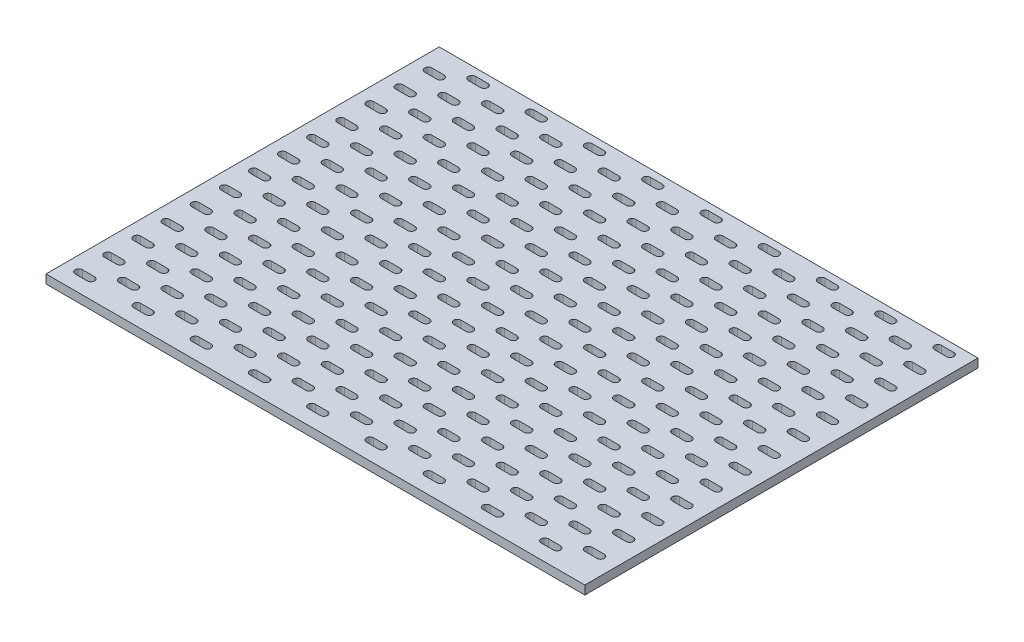
SolidWorks part; units mm, degrees
ref_plane "Спереди" through (0, 0, 0) normal (0, 0, 1) x (1, 0, 0)
ref_plane "Сверху" through (0, 0, 0) normal (0, 1, 0) x (1, 0, 0)
ref_plane "Справа" through (0, 0, 0) normal (1, 0, 0) x (0, 0, -1)
sketch "Эскиз1" plane through (0, 0, 0) normal (0, 1, 0) x (1, 0, 0)
  line L0 (-155, 130) -> (-146.6325, 130)
  line L1 (-185, 135) -> (185, 135)
  line L2 (-185, 135) -> (-185, -135)
  line L3 (-185, -135) -> (185, -135)
  line L4 (185, 135) -> (185, -135)
  line L5 (-185, 135) -> (185, -135) construction
  line L6 (-185, -135) -> (185, 135) construction
  line L7 (-155, 125) -> (-146.6325, 125)
  line L8 (-175, 115) -> (-166.6325, 115)
  line L9 (-175, 120) -> (-166.6325, 120)
  line L10 (-115, 130) -> (-106.6325, 130)
  line L11 (-115, 125) -> (-106.6325, 125)
  line L12 (-135, 115) -> (-126.6325, 115)
  line L13 (-135, 120) -> (-126.6325, 120)
  line L14 (-75, 130) -> (-66.6325, 130)
  line L15 (-75, 125) -> (-66.6325, 125)
  line L16 (-95, 115) -> (-86.6325, 115)
  line L17 (-95, 120) -> (-86.6325, 120)
  line L18 (-35, 130) -> (-26.6325, 130)
  line L19 (-35, 125) -> (-26.6325, 125)
  line L20 (-55, 115) -> (-46.6325, 115)
  line L21 (-55, 120) -> (-46.6325, 120)
  line L22 (5, 130) -> (13.3675, 130)
  line L23 (5, 125) -> (13.3675, 125)
  line L24 (-15, 115) -> (-6.6325, 115)
  line L25 (-15, 120) -> (-6.6325, 120)
  line L26 (45, 130) -> (53.3675, 130)
  line L27 (45, 125) -> (53.3675, 125)
  line L28 (25, 115) -> (33.3675, 115)
  line L29 (25, 120) -> (33.3675, 120)
  line L30 (85, 130) -> (93.3675, 130)
  line L31 (85, 125) -> (93.3675, 125)
  line L32 (65, 115) -> (73.3675, 115)
  line L33 (65, 120) -> (73.3675, 120)
  line L34 (125, 130) -> (133.3675, 130)
  line L35 (125, 125) -> (133.3675, 125)
  line L36 (105, 115) -> (113.3675, 115)
  line L37 (105, 120) -> (113.3675, 120)
  line L38 (165, 130) -> (173.3675, 130)
  line L39 (165, 125) -> (173.3675, 125)
  line L40 (145, 115) -> (153.3675, 115)
  line L41 (145, 120) -> (153.3675, 120)
  line L42 (-155, 110) -> (-146.6325, 110)
  line L43 (-155, 105) -> (-146.6325, 105)
  line L44 (-175, 95) -> (-166.6325, 95)
  line L45 (-175, 100) -> (-166.6325, 100)
  line L46 (-115, 110) -> (-106.6325, 110)
  line L47 (-115, 105) -> (-106.6325, 105)
  line L48 (-135, 95) -> (-126.6325, 95)
  line L49 (-135, 100) -> (-126.6325, 100)
  line L50 (-75, 110) -> (-66.6325, 110)
  line L51 (-75, 105) -> (-66.6325, 105)
  line L52 (-95, 95) -> (-86.6325, 95)
  line L53 (-95, 100) -> (-86.6325, 100)
  line L54 (-35, 110) -> (-26.6325, 110)
  line L55 (-35, 105) -> (-26.6325, 105)
  line L56 (-55, 95) -> (-46.6325, 95)
  line L57 (-55, 100) -> (-46.6325, 100)
  line L58 (5, 110) -> (13.3675, 110)
  line L59 (5, 105) -> (13.3675, 105)
  line L60 (-15, 95) -> (-6.6325, 95)
  line L61 (-15, 100) -> (-6.6325, 100)
  line L62 (45, 110) -> (53.3675, 110)
  line L63 (45, 105) -> (53.3675, 105)
  line L64 (25, 95) -> (33.3675, 95)
  line L65 (25, 100) -> (33.3675, 100)
  line L66 (85, 110) -> (93.3675, 110)
  line L67 (85, 105) -> (93.3675, 105)
  line L68 (65, 95) -> (73.3675, 95)
  line L69 (65, 100) -> (73.3675, 100)
  line L70 (125, 110) -> (133.3675, 110)
  line L71 (125, 105) -> (133.3675, 105)
  line L72 (105, 95) -> (113.3675, 95)
  line L73 (105, 100) -> (113.3675, 100)
  line L74 (165, 110) -> (173.3675, 110)
  line L75 (165, 105) -> (173.3675, 105)
  line L76 (145, 95) -> (153.3675, 95)
  line L77 (145, 100) -> (153.3675, 100)
  line L78 (-155, 90) -> (-146.6325, 90)
  line L79 (-155, 85) -> (-146.6325, 85)
  line L80 (-175, 75) -> (-166.6325, 75)
  line L81 (-175, 80) -> (-166.6325, 80)
  line L82 (-115, 90) -> (-106.6325, 90)
  line L83 (-115, 85) -> (-106.6325, 85)
  line L84 (-135, 75) -> (-126.6325, 75)
  line L85 (-135, 80) -> (-126.6325, 80)
  line L86 (-75, 90) -> (-66.6325, 90)
  line L87 (-75, 85) -> (-66.6325, 85)
  line L88 (-95, 75) -> (-86.6325, 75)
  line L89 (-95, 80) -> (-86.6325, 80)
  line L90 (-35, 90) -> (-26.6325, 90)
  line L91 (-35, 85) -> (-26.6325, 85)
  line L92 (-55, 75) -> (-46.6325, 75)
  line L93 (-55, 80) -> (-46.6325, 80)
  line L94 (5, 90) -> (13.3675, 90)
  line L95 (5, 85) -> (13.3675, 85)
  line L96 (-15, 75) -> (-6.6325, 75)
  line L97 (-15, 80) -> (-6.6325, 80)
  line L98 (45, 90) -> (53.3675, 90)
  line L99 (45, 85) -> (53.3675, 85)
  line L100 (25, 75) -> (33.3675, 75)
  line L101 (25, 80) -> (33.3675, 80)
  line L102 (85, 90) -> (93.3675, 90)
  line L103 (85, 85) -> (93.3675, 85)
  line L104 (65, 75) -> (73.3675, 75)
  line L105 (65, 80) -> (73.3675, 80)
  line L106 (125, 90) -> (133.3675, 90)
  line L107 (125, 85) -> (133.3675, 85)
  line L108 (105, 75) -> (113.3675, 75)
  line L109 (105, 80) -> (113.3675, 80)
  line L110 (165, 90) -> (173.3675, 90)
  line L111 (165, 85) -> (173.3675, 85)
  line L112 (145, 75) -> (153.3675, 75)
  line L113 (145, 80) -> (153.3675, 80)
  line L114 (-155, 70) -> (-146.6325, 70)
  line L115 (-155, 65) -> (-146.6325, 65)
  line L116 (-175, 55) -> (-166.6325, 55)
  line L117 (-175, 60) -> (-166.6325, 60)
  line L118 (-115, 70) -> (-106.6325, 70)
  line L119 (-115, 65) -> (-106.6325, 65)
  line L120 (-135, 55) -> (-126.6325, 55)
  line L121 (-135, 60) -> (-126.6325, 60)
  line L122 (-75, 70) -> (-66.6325, 70)
  line L123 (-75, 65) -> (-66.6325, 65)
  line L124 (-95, 55) -> (-86.6325, 55)
  line L125 (-95, 60) -> (-86.6325, 60)
  line L126 (-35, 70) -> (-26.6325, 70)
  line L127 (-35, 65) -> (-26.6325, 65)
  line L128 (-55, 55) -> (-46.6325, 55)
  line L129 (-55, 60) -> (-46.6325, 60)
  line L130 (5, 70) -> (13.3675, 70)
  line L131 (5, 65) -> (13.3675, 65)
  line L132 (-15, 55) -> (-6.6325, 55)
  line L133 (-15, 60) -> (-6.6325, 60)
  line L134 (45, 70) -> (53.3675, 70)
  line L135 (45, 65) -> (53.3675, 65)
  line L136 (25, 55) -> (33.3675, 55)
  line L137 (25, 60) -> (33.3675, 60)
  line L138 (85, 70) -> (93.3675, 70)
  line L139 (85, 65) -> (93.3675, 65)
  line L140 (65, 55) -> (73.3675, 55)
  line L141 (65, 60) -> (73.3675, 60)
  line L142 (125, 70) -> (133.3675, 70)
  line L143 (125, 65) -> (133.3675, 65)
  line L144 (105, 55) -> (113.3675, 55)
  line L145 (105, 60) -> (113.3675, 60)
  line L146 (165, 70) -> (173.3675, 70)
  line L147 (165, 65) -> (173.3675, 65)
  line L148 (145, 55) -> (153.3675, 55)
  line L149 (145, 60) -> (153.3675, 60)
  line L150 (-155, 50) -> (-146.6325, 50)
  line L151 (-155, 45) -> (-146.6325, 45)
  line L152 (-175, 35) -> (-166.6325, 35)
  line L153 (-175, 40) -> (-166.6325, 40)
  line L154 (-115, 50) -> (-106.6325, 50)
  line L155 (-115, 45) -> (-106.6325, 45)
  line L156 (-135, 35) -> (-126.6325, 35)
  line L157 (-135, 40) -> (-126.6325, 40)
  line L158 (-75, 50) -> (-66.6325, 50)
  line L159 (-75, 45) -> (-66.6325, 45)
  line L160 (-95, 35) -> (-86.6325, 35)
  line L161 (-95, 40) -> (-86.6325, 40)
  line L162 (-35, 50) -> (-26.6325, 50)
  line L163 (-35, 45) -> (-26.6325, 45)
  line L164 (-55, 35) -> (-46.6325, 35)
  line L165 (-55, 40) -> (-46.6325, 40)
  line L166 (5, 50) -> (13.3675, 50)
  line L167 (5, 45) -> (13.3675, 45)
  line L168 (-15, 35) -> (-6.6325, 35)
  line L169 (-15, 40) -> (-6.6325, 40)
  line L170 (45, 50) -> (53.3675, 50)
  line L171 (45, 45) -> (53.3675, 45)
  line L172 (25, 35) -> (33.3675, 35)
  line L173 (25, 40) -> (33.3675, 40)
  line L174 (85, 50) -> (93.3675, 50)
  line L175 (85, 45) -> (93.3675, 45)
  line L176 (65, 35) -> (73.3675, 35)
  line L177 (65, 40) -> (73.3675, 40)
  line L178 (125, 50) -> (133.3675, 50)
  line L179 (125, 45) -> (133.3675, 45)
  line L180 (105, 35) -> (113.3675, 35)
  line L181 (105, 40) -> (113.3675, 40)
  line L182 (165, 50) -> (173.3675, 50)
  line L183 (165, 45) -> (173.3675, 45)
  line L184 (145, 35) -> (153.3675, 35)
  line L185 (145, 40) -> (153.3675, 40)
  line L186 (-155, 30) -> (-146.6325, 30)
  line L187 (-155, 25) -> (-146.6325, 25)
  line L188 (-175, 15) -> (-166.6325, 15)
  line L189 (-175, 20) -> (-166.6325, 20)
  line L190 (-115, 30) -> (-106.6325, 30)
  line L191 (-115, 25) -> (-106.6325, 25)
  line L192 (-135, 15) -> (-126.6325, 15)
  line L193 (-135, 20) -> (-126.6325, 20)
  line L194 (-75, 30) -> (-66.6325, 30)
  line L195 (-75, 25) -> (-66.6325, 25)
  line L196 (-95, 15) -> (-86.6325, 15)
  line L197 (-95, 20) -> (-86.6325, 20)
  line L198 (-35, 30) -> (-26.6325, 30)
  line L199 (-35, 25) -> (-26.6325, 25)
  line L200 (-55, 15) -> (-46.6325, 15)
  line L201 (-55, 20) -> (-46.6325, 20)
  line L202 (5, 30) -> (13.3675, 30)
  line L203 (5, 25) -> (13.3675, 25)
  line L204 (-15, 15) -> (-6.6325, 15)
  line L205 (-15, 20) -> (-6.6325, 20)
  line L206 (45, 30) -> (53.3675, 30)
  line L207 (45, 25) -> (53.3675, 25)
  line L208 (25, 15) -> (33.3675, 15)
  line L209 (25, 20) -> (33.3675, 20)
  line L210 (85, 30) -> (93.3675, 30)
  line L211 (85, 25) -> (93.3675, 25)
  line L212 (65, 15) -> (73.3675, 15)
  line L213 (65, 20) -> (73.3675, 20)
  line L214 (125, 30) -> (133.3675, 30)
  line L215 (125, 25) -> (133.3675, 25)
  line L216 (105, 15) -> (113.3675, 15)
  line L217 (105, 20) -> (113.3675, 20)
  line L218 (165, 30) -> (173.3675, 30)
  line L219 (165, 25) -> (173.3675, 25)
  line L220 (145, 15) -> (153.3675, 15)
  line L221 (145, 20) -> (153.3675, 20)
  line L222 (-155, 10) -> (-146.6325, 10)
  line L223 (-155, 5) -> (-146.6325, 5)
  line L224 (-175, -5) -> (-166.6325, -5)
  line L225 (-175, 0) -> (-166.6325, 0)
  line L226 (-115, 10) -> (-106.6325, 10)
  line L227 (-115, 5) -> (-106.6325, 5)
  line L228 (-135, -5) -> (-126.6325, -5)
  line L229 (-135, 0) -> (-126.6325, 0)
  line L230 (-75, 10) -> (-66.6325, 10)
  line L231 (-75, 5) -> (-66.6325, 5)
  line L232 (-95, -5) -> (-86.6325, -5)
  line L233 (-95, 0) -> (-86.6325, 0)
  line L234 (-35, 10) -> (-26.6325, 10)
  line L235 (-35, 5) -> (-26.6325, 5)
  line L236 (-55, -5) -> (-46.6325, -5)
  line L237 (-55, 0) -> (-46.6325, 0)
  line L238 (5, 10) -> (13.3675, 10)
  line L239 (5, 5) -> (13.3675, 5)
  line L240 (-15, -5) -> (-6.6325, -5)
  line L241 (-15, 0) -> (-6.6325, 0)
  line L242 (45, 10) -> (53.3675, 10)
  line L243 (45, 5) -> (53.3675, 5)
  line L244 (25, -5) -> (33.3675, -5)
  line L245 (25, 0) -> (33.3675, 0)
  line L246 (85, 10) -> (93.3675, 10)
  line L247 (85, 5) -> (93.3675, 5)
  line L248 (65, -5) -> (73.3675, -5)
  line L249 (65, 0) -> (73.3675, 0)
  line L250 (125, 10) -> (133.3675, 10)
  line L251 (125, 5) -> (133.3675, 5)
  line L252 (105, -5) -> (113.3675, -5)
  line L253 (105, 0) -> (113.3675, 0)
  line L254 (165, 10) -> (173.3675, 10)
  line L255 (165, 5) -> (173.3675, 5)
  line L256 (145, -5) -> (153.3675, -5)
  line L257 (145, 0) -> (153.3675, 0)
  line L258 (-155, -10) -> (-146.6325, -10)
  line L259 (-155, -15) -> (-146.6325, -15)
  line L260 (-175, -25) -> (-166.6325, -25)
  line L261 (-175, -20) -> (-166.6325, -20)
  line L262 (-115, -10) -> (-106.6325, -10)
  line L263 (-115, -15) -> (-106.6325, -15)
  line L264 (-135, -25) -> (-126.6325, -25)
  line L265 (-135, -20) -> (-126.6325, -20)
  line L266 (-75, -10) -> (-66.6325, -10)
  line L267 (-75, -15) -> (-66.6325, -15)
  line L268 (-95, -25) -> (-86.6325, -25)
  line L269 (-95, -20) -> (-86.6325, -20)
  line L270 (-35, -10) -> (-26.6325, -10)
  line L271 (-35, -15) -> (-26.6325, -15)
  line L272 (-55, -25) -> (-46.6325, -25)
  line L273 (-55, -20) -> (-46.6325, -20)
  line L274 (5, -10) -> (13.3675, -10)
  line L275 (5, -15) -> (13.3675, -15)
  line L276 (-15, -25) -> (-6.6325, -25)
  line L277 (-15, -20) -> (-6.6325, -20)
  line L278 (45, -10) -> (53.3675, -10)
  line L279 (45, -15) -> (53.3675, -15)
  line L280 (25, -25) -> (33.3675, -25)
  line L281 (25, -20) -> (33.3675, -20)
  line L282 (85, -10) -> (93.3675, -10)
  line L283 (85, -15) -> (93.3675, -15)
  line L284 (65, -25) -> (73.3675, -25)
  line L285 (65, -20) -> (73.3675, -20)
  line L286 (125, -10) -> (133.3675, -10)
  line L287 (125, -15) -> (133.3675, -15)
  line L288 (105, -25) -> (113.3675, -25)
  line L289 (105, -20) -> (113.3675, -20)
  line L290 (165, -10) -> (173.3675, -10)
  line L291 (165, -15) -> (173.3675, -15)
  line L292 (145, -25) -> (153.3675, -25)
  line L293 (145, -20) -> (153.3675, -20)
  line L294 (-155, -30) -> (-146.6325, -30)
  line L295 (-155, -35) -> (-146.6325, -35)
  line L296 (-175, -45) -> (-166.6325, -45)
  line L297 (-175, -40) -> (-166.6325, -40)
  line L298 (-115, -30) -> (-106.6325, -30)
  line L299 (-115, -35) -> (-106.6325, -35)
  line L300 (-135, -45) -> (-126.6325, -45)
  line L301 (-135, -40) -> (-126.6325, -40)
  line L302 (-75, -30) -> (-66.6325, -30)
  line L303 (-75, -35) -> (-66.6325, -35)
  line L304 (-95, -45) -> (-86.6325, -45)
  line L305 (-95, -40) -> (-86.6325, -40)
  line L306 (-35, -30) -> (-26.6325, -30)
  line L307 (-35, -35) -> (-26.6325, -35)
  line L308 (-55, -45) -> (-46.6325, -45)
  line L309 (-55, -40) -> (-46.6325, -40)
  line L310 (5, -30) -> (13.3675, -30)
  line L311 (5, -35) -> (13.3675, -35)
  line L312 (-15, -45) -> (-6.6325, -45)
  line L313 (-15, -40) -> (-6.6325, -40)
  line L314 (45, -30) -> (53.3675, -30)
  line L315 (45, -35) -> (53.3675, -35)
  line L316 (25, -45) -> (33.3675, -45)
  line L317 (25, -40) -> (33.3675, -40)
  line L318 (85, -30) -> (93.3675, -30)
  line L319 (85, -35) -> (93.3675, -35)
  line L320 (65, -45) -> (73.3675, -45)
  line L321 (65, -40) -> (73.3675, -40)
  line L322 (125, -30) -> (133.3675, -30)
  line L323 (125, -35) -> (133.3675, -35)
  line L324 (105, -45) -> (113.3675, -45)
  line L325 (105, -40) -> (113.3675, -40)
  line L326 (165, -30) -> (173.3675, -30)
  line L327 (165, -35) -> (173.3675, -35)
  line L328 (145, -45) -> (153.3675, -45)
  line L329 (145, -40) -> (153.3675, -40)
  line L330 (-155, -50) -> (-146.6325, -50)
  line L331 (-155, -55) -> (-146.6325, -55)
  line L332 (-175, -65) -> (-166.6325, -65)
  line L333 (-175, -60) -> (-166.6325, -60)
  line L334 (-115, -50) -> (-106.6325, -50)
  line L335 (-115, -55) -> (-106.6325, -55)
  line L336 (-135, -65) -> (-126.6325, -65)
  line L337 (-135, -60) -> (-126.6325, -60)
  line L338 (-75, -50) -> (-66.6325, -50)
  line L339 (-75, -55) -> (-66.6325, -55)
  line L340 (-95, -65) -> (-86.6325, -65)
  line L341 (-95, -60) -> (-86.6325, -60)
  line L342 (-35, -50) -> (-26.6325, -50)
  line L343 (-35, -55) -> (-26.6325, -55)
  line L344 (-55, -65) -> (-46.6325, -65)
  line L345 (-55, -60) -> (-46.6325, -60)
  line L346 (5, -50) -> (13.3675, -50)
  line L347 (5, -55) -> (13.3675, -55)
  line L348 (-15, -65) -> (-6.6325, -65)
  line L349 (-15, -60) -> (-6.6325, -60)
  line L350 (45, -50) -> (53.3675, -50)
  line L351 (45, -55) -> (53.3675, -55)
  line L352 (25, -65) -> (33.3675, -65)
  line L353 (25, -60) -> (33.3675, -60)
  line L354 (85, -50) -> (93.3675, -50)
  line L355 (85, -55) -> (93.3675, -55)
  line L356 (65, -65) -> (73.3675, -65)
  line L357 (65, -60) -> (73.3675, -60)
  line L358 (125, -50) -> (133.3675, -50)
  line L359 (125, -55) -> (133.3675, -55)
  line L360 (105, -65) -> (113.3675, -65)
  line L361 (105, -60) -> (113.3675, -60)
  line L362 (165, -50) -> (173.3675, -50)
  line L363 (165, -55) -> (173.3675, -55)
  line L364 (145, -65) -> (153.3675, -65)
  line L365 (145, -60) -> (153.3675, -60)
  line L366 (-155, -70) -> (-146.6325, -70)
  line L367 (-155, -75) -> (-146.6325, -75)
  line L368 (-175, -85) -> (-166.6325, -85)
  line L369 (-175, -80) -> (-166.6325, -80)
  line L370 (-115, -70) -> (-106.6325, -70)
  line L371 (-115, -75) -> (-106.6325, -75)
  line L372 (-135, -85) -> (-126.6325, -85)
  line L373 (-135, -80) -> (-126.6325, -80)
  line L374 (-75, -70) -> (-66.6325, -70)
  line L375 (-75, -75) -> (-66.6325, -75)
  line L376 (-95, -85) -> (-86.6325, -85)
  line L377 (-95, -80) -> (-86.6325, -80)
  line L378 (-35, -70) -> (-26.6325, -70)
  line L379 (-35, -75) -> (-26.6325, -75)
  line L380 (-55, -85) -> (-46.6325, -85)
  line L381 (-55, -80) -> (-46.6325, -80)
  line L382 (5, -70) -> (13.3675, -70)
  line L383 (5, -75) -> (13.3675, -75)
  line L384 (-15, -85) -> (-6.6325, -85)
  line L385 (-15, -80) -> (-6.6325, -80)
  line L386 (45, -70) -> (53.3675, -70)
  line L387 (45, -75) -> (53.3675, -75)
  line L388 (25, -85) -> (33.3675, -85)
  line L389 (25, -80) -> (33.3675, -80)
  line L390 (85, -70) -> (93.3675, -70)
  line L391 (85, -75) -> (93.3675, -75)
  line L392 (65, -85) -> (73.3675, -85)
  line L393 (65, -80) -> (73.3675, -80)
  line L394 (125, -70) -> (133.3675, -70)
  line L395 (125, -75) -> (133.3675, -75)
  line L396 (105, -85) -> (113.3675, -85)
  line L397 (105, -80) -> (113.3675, -80)
  line L398 (165, -70) -> (173.3675, -70)
  line L399 (165, -75) -> (173.3675, -75)
  line L400 (145, -85) -> (153.3675, -85)
  line L401 (145, -80) -> (153.3675, -80)
  line L402 (-155, -90) -> (-146.6325, -90)
  line L403 (-155, -95) -> (-146.6325, -95)
  line L404 (-175, -105) -> (-166.6325, -105)
  line L405 (-175, -100) -> (-166.6325, -100)
  line L406 (-115, -90) -> (-106.6325, -90)
  line L407 (-115, -95) -> (-106.6325, -95)
  line L408 (-135, -105) -> (-126.6325, -105)
  line L409 (-135, -100) -> (-126.6325, -100)
  line L410 (-75, -90) -> (-66.6325, -90)
  line L411 (-75, -95) -> (-66.6325, -95)
  line L412 (-95, -105) -> (-86.6325, -105)
  line L413 (-95, -100) -> (-86.6325, -100)
  line L414 (-35, -90) -> (-26.6325, -90)
  line L415 (-35, -95) -> (-26.6325, -95)
  line L416 (-55, -105) -> (-46.6325, -105)
  line L417 (-55, -100) -> (-46.6325, -100)
  line L418 (5, -90) -> (13.3675, -90)
  line L419 (5, -95) -> (13.3675, -95)
  line L420 (-15, -105) -> (-6.6325, -105)
  line L421 (-15, -100) -> (-6.6325, -100)
  line L422 (45, -90) -> (53.3675, -90)
  line L423 (45, -95) -> (53.3675, -95)
  line L424 (25, -105) -> (33.3675, -105)
  line L425 (25, -100) -> (33.3675, -100)
  line L426 (85, -90) -> (93.3675, -90)
  line L427 (85, -95) -> (93.3675, -95)
  line L428 (65, -105) -> (73.3675, -105)
  line L429 (65, -100) -> (73.3675, -100)
  line L430 (125, -90) -> (133.3675, -90)
  line L431 (125, -95) -> (133.3675, -95)
  line L432 (105, -105) -> (113.3675, -105)
  line L433 (105, -100) -> (113.3675, -100)
  line L434 (165, -90) -> (173.3675, -90)
  line L435 (165, -95) -> (173.3675, -95)
  line L436 (145, -105) -> (153.3675, -105)
  line L437 (145, -100) -> (153.3675, -100)
  line L438 (-155, -110) -> (-146.6325, -110)
  line L439 (-155, -115) -> (-146.6325, -115)
  line L440 (-175, -125) -> (-166.6325, -125)
  line L441 (-175, -120) -> (-166.6325, -120)
  line L442 (-115, -110) -> (-106.6325, -110)
  line L443 (-115, -115) -> (-106.6325, -115)
  line L444 (-135, -125) -> (-126.6325, -125)
  line L445 (-135, -120) -> (-126.6325, -120)
  line L446 (-75, -110) -> (-66.6325, -110)
  line L447 (-75, -115) -> (-66.6325, -115)
  line L448 (-95, -125) -> (-86.6325, -125)
  line L449 (-95, -120) -> (-86.6325, -120)
  line L450 (-35, -110) -> (-26.6325, -110)
  line L451 (-35, -115) -> (-26.6325, -115)
  line L452 (-55, -125) -> (-46.6325, -125)
  line L453 (-55, -120) -> (-46.6325, -120)
  line L454 (5, -110) -> (13.3675, -110)
  line L455 (5, -115) -> (13.3675, -115)
  line L456 (-15, -125) -> (-6.6325, -125)
  line L457 (-15, -120) -> (-6.6325, -120)
  line L458 (45, -110) -> (53.3675, -110)
  line L459 (45, -115) -> (53.3675, -115)
  line L460 (25, -125) -> (33.3675, -125)
  line L461 (25, -120) -> (33.3675, -120)
  line L462 (85, -110) -> (93.3675, -110)
  line L463 (85, -115) -> (93.3675, -115)
  line L464 (65, -125) -> (73.3675, -125)
  line L465 (65, -120) -> (73.3675, -120)
  line L466 (125, -110) -> (133.3675, -110)
  line L467 (125, -115) -> (133.3675, -115)
  line L468 (105, -125) -> (113.3675, -125)
  line L469 (105, -120) -> (113.3675, -120)
  line L470 (165, -110) -> (173.3675, -110)
  line L471 (165, -115) -> (173.3675, -115)
  line L472 (145, -125) -> (153.3675, -125)
  line L473 (145, -120) -> (153.3675, -120)
  arc A0 (-146.6325, 125) -> (-146.6325, 130) centre (-146.6325, 127.5) ccw
  arc A1 (-155, 130) -> (-155, 125) centre (-155, 127.5) ccw
  arc A2 (-175, 120) -> (-175, 115) centre (-175, 117.5) ccw
  arc A3 (-166.6325, 115) -> (-166.6325, 120) centre (-166.6325, 117.5) ccw
  arc A4 (-106.6325, 125) -> (-106.6325, 130) centre (-106.6325, 127.5) ccw
  arc A5 (-115, 130) -> (-115, 125) centre (-115, 127.5) ccw
  arc A6 (-135, 120) -> (-135, 115) centre (-135, 117.5) ccw
  arc A7 (-126.6325, 115) -> (-126.6325, 120) centre (-126.6325, 117.5) ccw
  arc A8 (-66.6325, 125) -> (-66.6325, 130) centre (-66.6325, 127.5) ccw
  arc A9 (-75, 130) -> (-75, 125) centre (-75, 127.5) ccw
  arc A10 (-95, 120) -> (-95, 115) centre (-95, 117.5) ccw
  arc A11 (-86.6325, 115) -> (-86.6325, 120) centre (-86.6325, 117.5) ccw
  arc A12 (-26.6325, 125) -> (-26.6325, 130) centre (-26.6325, 127.5) ccw
  arc A13 (-35, 130) -> (-35, 125) centre (-35, 127.5) ccw
  arc A14 (-55, 120) -> (-55, 115) centre (-55, 117.5) ccw
  arc A15 (-46.6325, 115) -> (-46.6325, 120) centre (-46.6325, 117.5) ccw
  arc A16 (13.3675, 125) -> (13.3675, 130) centre (13.3675, 127.5) ccw
  arc A17 (5, 130) -> (5, 125) centre (5, 127.5) ccw
  arc A18 (-15, 120) -> (-15, 115) centre (-15, 117.5) ccw
  arc A19 (-6.6325, 115) -> (-6.6325, 120) centre (-6.6325, 117.5) ccw
  arc A20 (53.3675, 125) -> (53.3675, 130) centre (53.3675, 127.5) ccw
  arc A21 (45, 130) -> (45, 125) centre (45, 127.5) ccw
  arc A22 (25, 120) -> (25, 115) centre (25, 117.5) ccw
  arc A23 (33.3675, 115) -> (33.3675, 120) centre (33.3675, 117.5) ccw
  arc A24 (93.3675, 125) -> (93.3675, 130) centre (93.3675, 127.5) ccw
  arc A25 (85, 130) -> (85, 125) centre (85, 127.5) ccw
  arc A26 (65, 120) -> (65, 115) centre (65, 117.5) ccw
  arc A27 (73.3675, 115) -> (73.3675, 120) centre (73.3675, 117.5) ccw
  arc A28 (133.3675, 125) -> (133.3675, 130) centre (133.3675, 127.5) ccw
  arc A29 (125, 130) -> (125, 125) centre (125, 127.5) ccw
  arc A30 (105, 120) -> (105, 115) centre (105, 117.5) ccw
  arc A31 (113.3675, 115) -> (113.3675, 120) centre (113.3675, 117.5) ccw
  arc A32 (173.3675, 125) -> (173.3675, 130) centre (173.3675, 127.5) ccw
  arc A33 (165, 130) -> (165, 125) centre (165, 127.5) ccw
  arc A34 (145, 120) -> (145, 115) centre (145, 117.5) ccw
  arc A35 (153.3675, 115) -> (153.3675, 120) centre (153.3675, 117.5) ccw
  arc A36 (-146.6325, 105) -> (-146.6325, 110) centre (-146.6325, 107.5) ccw
  arc A37 (-155, 110) -> (-155, 105) centre (-155, 107.5) ccw
  arc A38 (-175, 100) -> (-175, 95) centre (-175, 97.5) ccw
  arc A39 (-166.6325, 95) -> (-166.6325, 100) centre (-166.6325, 97.5) ccw
  arc A40 (-106.6325, 105) -> (-106.6325, 110) centre (-106.6325, 107.5) ccw
  arc A41 (-115, 110) -> (-115, 105) centre (-115, 107.5) ccw
  arc A42 (-135, 100) -> (-135, 95) centre (-135, 97.5) ccw
  arc A43 (-126.6325, 95) -> (-126.6325, 100) centre (-126.6325, 97.5) ccw
  arc A44 (-66.6325, 105) -> (-66.6325, 110) centre (-66.6325, 107.5) ccw
  arc A45 (-75, 110) -> (-75, 105) centre (-75, 107.5) ccw
  arc A46 (-95, 100) -> (-95, 95) centre (-95, 97.5) ccw
  arc A47 (-86.6325, 95) -> (-86.6325, 100) centre (-86.6325, 97.5) ccw
  arc A48 (-26.6325, 105) -> (-26.6325, 110) centre (-26.6325, 107.5) ccw
  arc A49 (-35, 110) -> (-35, 105) centre (-35, 107.5) ccw
  arc A50 (-55, 100) -> (-55, 95) centre (-55, 97.5) ccw
  arc A51 (-46.6325, 95) -> (-46.6325, 100) centre (-46.6325, 97.5) ccw
  arc A52 (13.3675, 105) -> (13.3675, 110) centre (13.3675, 107.5) ccw
  arc A53 (5, 110) -> (5, 105) centre (5, 107.5) ccw
  arc A54 (-15, 100) -> (-15, 95) centre (-15, 97.5) ccw
  arc A55 (-6.6325, 95) -> (-6.6325, 100) centre (-6.6325, 97.5) ccw
  arc A56 (53.3675, 105) -> (53.3675, 110) centre (53.3675, 107.5) ccw
  arc A57 (45, 110) -> (45, 105) centre (45, 107.5) ccw
  arc A58 (25, 100) -> (25, 95) centre (25, 97.5) ccw
  arc A59 (33.3675, 95) -> (33.3675, 100) centre (33.3675, 97.5) ccw
  arc A60 (93.3675, 105) -> (93.3675, 110) centre (93.3675, 107.5) ccw
  arc A61 (85, 110) -> (85, 105) centre (85, 107.5) ccw
  arc A62 (65, 100) -> (65, 95) centre (65, 97.5) ccw
  arc A63 (73.3675, 95) -> (73.3675, 100) centre (73.3675, 97.5) ccw
  arc A64 (133.3675, 105) -> (133.3675, 110) centre (133.3675, 107.5) ccw
  arc A65 (125, 110) -> (125, 105) centre (125, 107.5) ccw
  arc A66 (105, 100) -> (105, 95) centre (105, 97.5) ccw
  arc A67 (113.3675, 95) -> (113.3675, 100) centre (113.3675, 97.5) ccw
  arc A68 (173.3675, 105) -> (173.3675, 110) centre (173.3675, 107.5) ccw
  arc A69 (165, 110) -> (165, 105) centre (165, 107.5) ccw
  arc A70 (145, 100) -> (145, 95) centre (145, 97.5) ccw
  arc A71 (153.3675, 95) -> (153.3675, 100) centre (153.3675, 97.5) ccw
  arc A72 (-146.6325, 85) -> (-146.6325, 90) centre (-146.6325, 87.5) ccw
  arc A73 (-155, 90) -> (-155, 85) centre (-155, 87.5) ccw
  arc A74 (-175, 80) -> (-175, 75) centre (-175, 77.5) ccw
  arc A75 (-166.6325, 75) -> (-166.6325, 80) centre (-166.6325, 77.5) ccw
  arc A76 (-106.6325, 85) -> (-106.6325, 90) centre (-106.6325, 87.5) ccw
  arc A77 (-115, 90) -> (-115, 85) centre (-115, 87.5) ccw
  arc A78 (-135, 80) -> (-135, 75) centre (-135, 77.5) ccw
  arc A79 (-126.6325, 75) -> (-126.6325, 80) centre (-126.6325, 77.5) ccw
  arc A80 (-66.6325, 85) -> (-66.6325, 90) centre (-66.6325, 87.5) ccw
  arc A81 (-75, 90) -> (-75, 85) centre (-75, 87.5) ccw
  arc A82 (-95, 80) -> (-95, 75) centre (-95, 77.5) ccw
  arc A83 (-86.6325, 75) -> (-86.6325, 80) centre (-86.6325, 77.5) ccw
  arc A84 (-26.6325, 85) -> (-26.6325, 90) centre (-26.6325, 87.5) ccw
  arc A85 (-35, 90) -> (-35, 85) centre (-35, 87.5) ccw
  arc A86 (-55, 80) -> (-55, 75) centre (-55, 77.5) ccw
  arc A87 (-46.6325, 75) -> (-46.6325, 80) centre (-46.6325, 77.5) ccw
  arc A88 (13.3675, 85) -> (13.3675, 90) centre (13.3675, 87.5) ccw
  arc A89 (5, 90) -> (5, 85) centre (5, 87.5) ccw
  arc A90 (-15, 80) -> (-15, 75) centre (-15, 77.5) ccw
  arc A91 (-6.6325, 75) -> (-6.6325, 80) centre (-6.6325, 77.5) ccw
  arc A92 (53.3675, 85) -> (53.3675, 90) centre (53.3675, 87.5) ccw
  arc A93 (45, 90) -> (45, 85) centre (45, 87.5) ccw
  arc A94 (25, 80) -> (25, 75) centre (25, 77.5) ccw
  arc A95 (33.3675, 75) -> (33.3675, 80) centre (33.3675, 77.5) ccw
  arc A96 (93.3675, 85) -> (93.3675, 90) centre (93.3675, 87.5) ccw
  arc A97 (85, 90) -> (85, 85) centre (85, 87.5) ccw
  arc A98 (65, 80) -> (65, 75) centre (65, 77.5) ccw
  arc A99 (73.3675, 75) -> (73.3675, 80) centre (73.3675, 77.5) ccw
  arc A100 (133.3675, 85) -> (133.3675, 90) centre (133.3675, 87.5) ccw
  arc A101 (125, 90) -> (125, 85) centre (125, 87.5) ccw
  arc A102 (105, 80) -> (105, 75) centre (105, 77.5) ccw
  arc A103 (113.3675, 75) -> (113.3675, 80) centre (113.3675, 77.5) ccw
  arc A104 (173.3675, 85) -> (173.3675, 90) centre (173.3675, 87.5) ccw
  arc A105 (165, 90) -> (165, 85) centre (165, 87.5) ccw
  arc A106 (145, 80) -> (145, 75) centre (145, 77.5) ccw
  arc A107 (153.3675, 75) -> (153.3675, 80) centre (153.3675, 77.5) ccw
  arc A108 (-146.6325, 65) -> (-146.6325, 70) centre (-146.6325, 67.5) ccw
  arc A109 (-155, 70) -> (-155, 65) centre (-155, 67.5) ccw
  arc A110 (-175, 60) -> (-175, 55) centre (-175, 57.5) ccw
  arc A111 (-166.6325, 55) -> (-166.6325, 60) centre (-166.6325, 57.5) ccw
  arc A112 (-106.6325, 65) -> (-106.6325, 70) centre (-106.6325, 67.5) ccw
  arc A113 (-115, 70) -> (-115, 65) centre (-115, 67.5) ccw
  arc A114 (-135, 60) -> (-135, 55) centre (-135, 57.5) ccw
  arc A115 (-126.6325, 55) -> (-126.6325, 60) centre (-126.6325, 57.5) ccw
  arc A116 (-66.6325, 65) -> (-66.6325, 70) centre (-66.6325, 67.5) ccw
  arc A117 (-75, 70) -> (-75, 65) centre (-75, 67.5) ccw
  arc A118 (-95, 60) -> (-95, 55) centre (-95, 57.5) ccw
  arc A119 (-86.6325, 55) -> (-86.6325, 60) centre (-86.6325, 57.5) ccw
  arc A120 (-26.6325, 65) -> (-26.6325, 70) centre (-26.6325, 67.5) ccw
  arc A121 (-35, 70) -> (-35, 65) centre (-35, 67.5) ccw
  arc A122 (-55, 60) -> (-55, 55) centre (-55, 57.5) ccw
  arc A123 (-46.6325, 55) -> (-46.6325, 60) centre (-46.6325, 57.5) ccw
  arc A124 (13.3675, 65) -> (13.3675, 70) centre (13.3675, 67.5) ccw
  arc A125 (5, 70) -> (5, 65) centre (5, 67.5) ccw
  arc A126 (-15, 60) -> (-15, 55) centre (-15, 57.5) ccw
  arc A127 (-6.6325, 55) -> (-6.6325, 60) centre (-6.6325, 57.5) ccw
  arc A128 (53.3675, 65) -> (53.3675, 70) centre (53.3675, 67.5) ccw
  arc A129 (45, 70) -> (45, 65) centre (45, 67.5) ccw
  arc A130 (25, 60) -> (25, 55) centre (25, 57.5) ccw
  arc A131 (33.3675, 55) -> (33.3675, 60) centre (33.3675, 57.5) ccw
  arc A132 (93.3675, 65) -> (93.3675, 70) centre (93.3675, 67.5) ccw
  arc A133 (85, 70) -> (85, 65) centre (85, 67.5) ccw
  arc A134 (65, 60) -> (65, 55) centre (65, 57.5) ccw
  arc A135 (73.3675, 55) -> (73.3675, 60) centre (73.3675, 57.5) ccw
  arc A136 (133.3675, 65) -> (133.3675, 70) centre (133.3675, 67.5) ccw
  arc A137 (125, 70) -> (125, 65) centre (125, 67.5) ccw
  arc A138 (105, 60) -> (105, 55) centre (105, 57.5) ccw
  arc A139 (113.3675, 55) -> (113.3675, 60) centre (113.3675, 57.5) ccw
  arc A140 (173.3675, 65) -> (173.3675, 70) centre (173.3675, 67.5) ccw
  arc A141 (165, 70) -> (165, 65) centre (165, 67.5) ccw
  arc A142 (145, 60) -> (145, 55) centre (145, 57.5) ccw
  arc A143 (153.3675, 55) -> (153.3675, 60) centre (153.3675, 57.5) ccw
  arc A144 (-146.6325, 45) -> (-146.6325, 50) centre (-146.6325, 47.5) ccw
  arc A145 (-155, 50) -> (-155, 45) centre (-155, 47.5) ccw
  arc A146 (-175, 40) -> (-175, 35) centre (-175, 37.5) ccw
  arc A147 (-166.6325, 35) -> (-166.6325, 40) centre (-166.6325, 37.5) ccw
  arc A148 (-106.6325, 45) -> (-106.6325, 50) centre (-106.6325, 47.5) ccw
  arc A149 (-115, 50) -> (-115, 45) centre (-115, 47.5) ccw
  arc A150 (-135, 40) -> (-135, 35) centre (-135, 37.5) ccw
  arc A151 (-126.6325, 35) -> (-126.6325, 40) centre (-126.6325, 37.5) ccw
  arc A152 (-66.6325, 45) -> (-66.6325, 50) centre (-66.6325, 47.5) ccw
  arc A153 (-75, 50) -> (-75, 45) centre (-75, 47.5) ccw
  arc A154 (-95, 40) -> (-95, 35) centre (-95, 37.5) ccw
  arc A155 (-86.6325, 35) -> (-86.6325, 40) centre (-86.6325, 37.5) ccw
  arc A156 (-26.6325, 45) -> (-26.6325, 50) centre (-26.6325, 47.5) ccw
  arc A157 (-35, 50) -> (-35, 45) centre (-35, 47.5) ccw
  arc A158 (-55, 40) -> (-55, 35) centre (-55, 37.5) ccw
  arc A159 (-46.6325, 35) -> (-46.6325, 40) centre (-46.6325, 37.5) ccw
  arc A160 (13.3675, 45) -> (13.3675, 50) centre (13.3675, 47.5) ccw
  arc A161 (5, 50) -> (5, 45) centre (5, 47.5) ccw
  arc A162 (-15, 40) -> (-15, 35) centre (-15, 37.5) ccw
  arc A163 (-6.6325, 35) -> (-6.6325, 40) centre (-6.6325, 37.5) ccw
  arc A164 (53.3675, 45) -> (53.3675, 50) centre (53.3675, 47.5) ccw
  arc A165 (45, 50) -> (45, 45) centre (45, 47.5) ccw
  arc A166 (25, 40) -> (25, 35) centre (25, 37.5) ccw
  arc A167 (33.3675, 35) -> (33.3675, 40) centre (33.3675, 37.5) ccw
  arc A168 (93.3675, 45) -> (93.3675, 50) centre (93.3675, 47.5) ccw
  arc A169 (85, 50) -> (85, 45) centre (85, 47.5) ccw
  arc A170 (65, 40) -> (65, 35) centre (65, 37.5) ccw
  arc A171 (73.3675, 35) -> (73.3675, 40) centre (73.3675, 37.5) ccw
  arc A172 (133.3675, 45) -> (133.3675, 50) centre (133.3675, 47.5) ccw
  arc A173 (125, 50) -> (125, 45) centre (125, 47.5) ccw
  arc A174 (105, 40) -> (105, 35) centre (105, 37.5) ccw
  arc A175 (113.3675, 35) -> (113.3675, 40) centre (113.3675, 37.5) ccw
  arc A176 (173.3675, 45) -> (173.3675, 50) centre (173.3675, 47.5) ccw
  arc A177 (165, 50) -> (165, 45) centre (165, 47.5) ccw
  arc A178 (145, 40) -> (145, 35) centre (145, 37.5) ccw
  arc A179 (153.3675, 35) -> (153.3675, 40) centre (153.3675, 37.5) ccw
  arc A180 (-146.6325, 25) -> (-146.6325, 30) centre (-146.6325, 27.5) ccw
  arc A181 (-155, 30) -> (-155, 25) centre (-155, 27.5) ccw
  arc A182 (-175, 20) -> (-175, 15) centre (-175, 17.5) ccw
  arc A183 (-166.6325, 15) -> (-166.6325, 20) centre (-166.6325, 17.5) ccw
  arc A184 (-106.6325, 25) -> (-106.6325, 30) centre (-106.6325, 27.5) ccw
  arc A185 (-115, 30) -> (-115, 25) centre (-115, 27.5) ccw
  arc A186 (-135, 20) -> (-135, 15) centre (-135, 17.5) ccw
  arc A187 (-126.6325, 15) -> (-126.6325, 20) centre (-126.6325, 17.5) ccw
  arc A188 (-66.6325, 25) -> (-66.6325, 30) centre (-66.6325, 27.5) ccw
  arc A189 (-75, 30) -> (-75, 25) centre (-75, 27.5) ccw
  arc A190 (-95, 20) -> (-95, 15) centre (-95, 17.5) ccw
  arc A191 (-86.6325, 15) -> (-86.6325, 20) centre (-86.6325, 17.5) ccw
  arc A192 (-26.6325, 25) -> (-26.6325, 30) centre (-26.6325, 27.5) ccw
  arc A193 (-35, 30) -> (-35, 25) centre (-35, 27.5) ccw
  arc A194 (-55, 20) -> (-55, 15) centre (-55, 17.5) ccw
  arc A195 (-46.6325, 15) -> (-46.6325, 20) centre (-46.6325, 17.5) ccw
  arc A196 (13.3675, 25) -> (13.3675, 30) centre (13.3675, 27.5) ccw
  arc A197 (5, 30) -> (5, 25) centre (5, 27.5) ccw
  arc A198 (-15, 20) -> (-15, 15) centre (-15, 17.5) ccw
  arc A199 (-6.6325, 15) -> (-6.6325, 20) centre (-6.6325, 17.5) ccw
  arc A200 (53.3675, 25) -> (53.3675, 30) centre (53.3675, 27.5) ccw
  arc A201 (45, 30) -> (45, 25) centre (45, 27.5) ccw
  arc A202 (25, 20) -> (25, 15) centre (25, 17.5) ccw
  arc A203 (33.3675, 15) -> (33.3675, 20) centre (33.3675, 17.5) ccw
  arc A204 (93.3675, 25) -> (93.3675, 30) centre (93.3675, 27.5) ccw
  arc A205 (85, 30) -> (85, 25) centre (85, 27.5) ccw
  arc A206 (65, 20) -> (65, 15) centre (65, 17.5) ccw
  arc A207 (73.3675, 15) -> (73.3675, 20) centre (73.3675, 17.5) ccw
  arc A208 (133.3675, 25) -> (133.3675, 30) centre (133.3675, 27.5) ccw
  arc A209 (125, 30) -> (125, 25) centre (125, 27.5) ccw
  arc A210 (105, 20) -> (105, 15) centre (105, 17.5) ccw
  arc A211 (113.3675, 15) -> (113.3675, 20) centre (113.3675, 17.5) ccw
  arc A212 (173.3675, 25) -> (173.3675, 30) centre (173.3675, 27.5) ccw
  arc A213 (165, 30) -> (165, 25) centre (165, 27.5) ccw
  arc A214 (145, 20) -> (145, 15) centre (145, 17.5) ccw
  arc A215 (153.3675, 15) -> (153.3675, 20) centre (153.3675, 17.5) ccw
  arc A216 (-146.6325, 5) -> (-146.6325, 10) centre (-146.6325, 7.5) ccw
  arc A217 (-155, 10) -> (-155, 5) centre (-155, 7.5) ccw
  arc A218 (-175, 0) -> (-175, -5) centre (-175, -2.5) ccw
  arc A219 (-166.6325, -5) -> (-166.6325, 0) centre (-166.6325, -2.5) ccw
  arc A220 (-106.6325, 5) -> (-106.6325, 10) centre (-106.6325, 7.5) ccw
  arc A221 (-115, 10) -> (-115, 5) centre (-115, 7.5) ccw
  arc A222 (-135, 0) -> (-135, -5) centre (-135, -2.5) ccw
  arc A223 (-126.6325, -5) -> (-126.6325, 0) centre (-126.6325, -2.5) ccw
  arc A224 (-66.6325, 5) -> (-66.6325, 10) centre (-66.6325, 7.5) ccw
  arc A225 (-75, 10) -> (-75, 5) centre (-75, 7.5) ccw
  arc A226 (-95, 0) -> (-95, -5) centre (-95, -2.5) ccw
  arc A227 (-86.6325, -5) -> (-86.6325, 0) centre (-86.6325, -2.5) ccw
  arc A228 (-26.6325, 5) -> (-26.6325, 10) centre (-26.6325, 7.5) ccw
  arc A229 (-35, 10) -> (-35, 5) centre (-35, 7.5) ccw
  arc A230 (-55, 0) -> (-55, -5) centre (-55, -2.5) ccw
  arc A231 (-46.6325, -5) -> (-46.6325, 0) centre (-46.6325, -2.5) ccw
  arc A232 (13.3675, 5) -> (13.3675, 10) centre (13.3675, 7.5) ccw
  arc A233 (5, 10) -> (5, 5) centre (5, 7.5) ccw
  arc A234 (-15, 0) -> (-15, -5) centre (-15, -2.5) ccw
  arc A235 (-6.6325, -5) -> (-6.6325, 0) centre (-6.6325, -2.5) ccw
  arc A236 (53.3675, 5) -> (53.3675, 10) centre (53.3675, 7.5) ccw
  arc A237 (45, 10) -> (45, 5) centre (45, 7.5) ccw
  arc A238 (25, 0) -> (25, -5) centre (25, -2.5) ccw
  arc A239 (33.3675, -5) -> (33.3675, 0) centre (33.3675, -2.5) ccw
  arc A240 (93.3675, 5) -> (93.3675, 10) centre (93.3675, 7.5) ccw
  arc A241 (85, 10) -> (85, 5) centre (85, 7.5) ccw
  arc A242 (65, 0) -> (65, -5) centre (65, -2.5) ccw
  arc A243 (73.3675, -5) -> (73.3675, 0) centre (73.3675, -2.5) ccw
  arc A244 (133.3675, 5) -> (133.3675, 10) centre (133.3675, 7.5) ccw
  arc A245 (125, 10) -> (125, 5) centre (125, 7.5) ccw
  arc A246 (105, 0) -> (105, -5) centre (105, -2.5) ccw
  arc A247 (113.3675, -5) -> (113.3675, 0) centre (113.3675, -2.5) ccw
  arc A248 (173.3675, 5) -> (173.3675, 10) centre (173.3675, 7.5) ccw
  arc A249 (165, 10) -> (165, 5) centre (165, 7.5) ccw
  arc A250 (145, 0) -> (145, -5) centre (145, -2.5) ccw
  arc A251 (153.3675, -5) -> (153.3675, 0) centre (153.3675, -2.5) ccw
  arc A252 (-146.6325, -15) -> (-146.6325, -10) centre (-146.6325, -12.5) ccw
  arc A253 (-155, -10) -> (-155, -15) centre (-155, -12.5) ccw
  arc A254 (-175, -20) -> (-175, -25) centre (-175, -22.5) ccw
  arc A255 (-166.6325, -25) -> (-166.6325, -20) centre (-166.6325, -22.5) ccw
  arc A256 (-106.6325, -15) -> (-106.6325, -10) centre (-106.6325, -12.5) ccw
  arc A257 (-115, -10) -> (-115, -15) centre (-115, -12.5) ccw
  arc A258 (-135, -20) -> (-135, -25) centre (-135, -22.5) ccw
  arc A259 (-126.6325, -25) -> (-126.6325, -20) centre (-126.6325, -22.5) ccw
  arc A260 (-66.6325, -15) -> (-66.6325, -10) centre (-66.6325, -12.5) ccw
  arc A261 (-75, -10) -> (-75, -15) centre (-75, -12.5) ccw
  arc A262 (-95, -20) -> (-95, -25) centre (-95, -22.5) ccw
  arc A263 (-86.6325, -25) -> (-86.6325, -20) centre (-86.6325, -22.5) ccw
  arc A264 (-26.6325, -15) -> (-26.6325, -10) centre (-26.6325, -12.5) ccw
  arc A265 (-35, -10) -> (-35, -15) centre (-35, -12.5) ccw
  arc A266 (-55, -20) -> (-55, -25) centre (-55, -22.5) ccw
  arc A267 (-46.6325, -25) -> (-46.6325, -20) centre (-46.6325, -22.5) ccw
  arc A268 (13.3675, -15) -> (13.3675, -10) centre (13.3675, -12.5) ccw
  arc A269 (5, -10) -> (5, -15) centre (5, -12.5) ccw
  arc A270 (-15, -20) -> (-15, -25) centre (-15, -22.5) ccw
  arc A271 (-6.6325, -25) -> (-6.6325, -20) centre (-6.6325, -22.5) ccw
  arc A272 (53.3675, -15) -> (53.3675, -10) centre (53.3675, -12.5) ccw
  arc A273 (45, -10) -> (45, -15) centre (45, -12.5) ccw
  arc A274 (25, -20) -> (25, -25) centre (25, -22.5) ccw
  arc A275 (33.3675, -25) -> (33.3675, -20) centre (33.3675, -22.5) ccw
  arc A276 (93.3675, -15) -> (93.3675, -10) centre (93.3675, -12.5) ccw
  arc A277 (85, -10) -> (85, -15) centre (85, -12.5) ccw
  arc A278 (65, -20) -> (65, -25) centre (65, -22.5) ccw
  arc A279 (73.3675, -25) -> (73.3675, -20) centre (73.3675, -22.5) ccw
  arc A280 (133.3675, -15) -> (133.3675, -10) centre (133.3675, -12.5) ccw
  arc A281 (125, -10) -> (125, -15) centre (125, -12.5) ccw
  arc A282 (105, -20) -> (105, -25) centre (105, -22.5) ccw
  arc A283 (113.3675, -25) -> (113.3675, -20) centre (113.3675, -22.5) ccw
  arc A284 (173.3675, -15) -> (173.3675, -10) centre (173.3675, -12.5) ccw
  arc A285 (165, -10) -> (165, -15) centre (165, -12.5) ccw
  arc A286 (145, -20) -> (145, -25) centre (145, -22.5) ccw
  arc A287 (153.3675, -25) -> (153.3675, -20) centre (153.3675, -22.5) ccw
  arc A288 (-146.6325, -35) -> (-146.6325, -30) centre (-146.6325, -32.5) ccw
  arc A289 (-155, -30) -> (-155, -35) centre (-155, -32.5) ccw
  arc A290 (-175, -40) -> (-175, -45) centre (-175, -42.5) ccw
  arc A291 (-166.6325, -45) -> (-166.6325, -40) centre (-166.6325, -42.5) ccw
  arc A292 (-106.6325, -35) -> (-106.6325, -30) centre (-106.6325, -32.5) ccw
  arc A293 (-115, -30) -> (-115, -35) centre (-115, -32.5) ccw
  arc A294 (-135, -40) -> (-135, -45) centre (-135, -42.5) ccw
  arc A295 (-126.6325, -45) -> (-126.6325, -40) centre (-126.6325, -42.5) ccw
  arc A296 (-66.6325, -35) -> (-66.6325, -30) centre (-66.6325, -32.5) ccw
  arc A297 (-75, -30) -> (-75, -35) centre (-75, -32.5) ccw
  arc A298 (-95, -40) -> (-95, -45) centre (-95, -42.5) ccw
  arc A299 (-86.6325, -45) -> (-86.6325, -40) centre (-86.6325, -42.5) ccw
  arc A300 (-26.6325, -35) -> (-26.6325, -30) centre (-26.6325, -32.5) ccw
  arc A301 (-35, -30) -> (-35, -35) centre (-35, -32.5) ccw
  arc A302 (-55, -40) -> (-55, -45) centre (-55, -42.5) ccw
  arc A303 (-46.6325, -45) -> (-46.6325, -40) centre (-46.6325, -42.5) ccw
  arc A304 (13.3675, -35) -> (13.3675, -30) centre (13.3675, -32.5) ccw
  arc A305 (5, -30) -> (5, -35) centre (5, -32.5) ccw
  arc A306 (-15, -40) -> (-15, -45) centre (-15, -42.5) ccw
  arc A307 (-6.6325, -45) -> (-6.6325, -40) centre (-6.6325, -42.5) ccw
  arc A308 (53.3675, -35) -> (53.3675, -30) centre (53.3675, -32.5) ccw
  arc A309 (45, -30) -> (45, -35) centre (45, -32.5) ccw
  arc A310 (25, -40) -> (25, -45) centre (25, -42.5) ccw
  arc A311 (33.3675, -45) -> (33.3675, -40) centre (33.3675, -42.5) ccw
  arc A312 (93.3675, -35) -> (93.3675, -30) centre (93.3675, -32.5) ccw
  arc A313 (85, -30) -> (85, -35) centre (85, -32.5) ccw
  arc A314 (65, -40) -> (65, -45) centre (65, -42.5) ccw
  arc A315 (73.3675, -45) -> (73.3675, -40) centre (73.3675, -42.5) ccw
  arc A316 (133.3675, -35) -> (133.3675, -30) centre (133.3675, -32.5) ccw
  arc A317 (125, -30) -> (125, -35) centre (125, -32.5) ccw
  arc A318 (105, -40) -> (105, -45) centre (105, -42.5) ccw
  arc A319 (113.3675, -45) -> (113.3675, -40) centre (113.3675, -42.5) ccw
  arc A320 (173.3675, -35) -> (173.3675, -30) centre (173.3675, -32.5) ccw
  arc A321 (165, -30) -> (165, -35) centre (165, -32.5) ccw
  arc A322 (145, -40) -> (145, -45) centre (145, -42.5) ccw
  arc A323 (153.3675, -45) -> (153.3675, -40) centre (153.3675, -42.5) ccw
  arc A324 (-146.6325, -55) -> (-146.6325, -50) centre (-146.6325, -52.5) ccw
  arc A325 (-155, -50) -> (-155, -55) centre (-155, -52.5) ccw
  arc A326 (-175, -60) -> (-175, -65) centre (-175, -62.5) ccw
  arc A327 (-166.6325, -65) -> (-166.6325, -60) centre (-166.6325, -62.5) ccw
  arc A328 (-106.6325, -55) -> (-106.6325, -50) centre (-106.6325, -52.5) ccw
  arc A329 (-115, -50) -> (-115, -55) centre (-115, -52.5) ccw
  arc A330 (-135, -60) -> (-135, -65) centre (-135, -62.5) ccw
  arc A331 (-126.6325, -65) -> (-126.6325, -60) centre (-126.6325, -62.5) ccw
  arc A332 (-66.6325, -55) -> (-66.6325, -50) centre (-66.6325, -52.5) ccw
  arc A333 (-75, -50) -> (-75, -55) centre (-75, -52.5) ccw
  arc A334 (-95, -60) -> (-95, -65) centre (-95, -62.5) ccw
  arc A335 (-86.6325, -65) -> (-86.6325, -60) centre (-86.6325, -62.5) ccw
  arc A336 (-26.6325, -55) -> (-26.6325, -50) centre (-26.6325, -52.5) ccw
  arc A337 (-35, -50) -> (-35, -55) centre (-35, -52.5) ccw
  arc A338 (-55, -60) -> (-55, -65) centre (-55, -62.5) ccw
  arc A339 (-46.6325, -65) -> (-46.6325, -60) centre (-46.6325, -62.5) ccw
  arc A340 (13.3675, -55) -> (13.3675, -50) centre (13.3675, -52.5) ccw
  arc A341 (5, -50) -> (5, -55) centre (5, -52.5) ccw
  arc A342 (-15, -60) -> (-15, -65) centre (-15, -62.5) ccw
  arc A343 (-6.6325, -65) -> (-6.6325, -60) centre (-6.6325, -62.5) ccw
  arc A344 (53.3675, -55) -> (53.3675, -50) centre (53.3675, -52.5) ccw
  arc A345 (45, -50) -> (45, -55) centre (45, -52.5) ccw
  arc A346 (25, -60) -> (25, -65) centre (25, -62.5) ccw
  arc A347 (33.3675, -65) -> (33.3675, -60) centre (33.3675, -62.5) ccw
  arc A348 (93.3675, -55) -> (93.3675, -50) centre (93.3675, -52.5) ccw
  arc A349 (85, -50) -> (85, -55) centre (85, -52.5) ccw
  arc A350 (65, -60) -> (65, -65) centre (65, -62.5) ccw
  arc A351 (73.3675, -65) -> (73.3675, -60) centre (73.3675, -62.5) ccw
  arc A352 (133.3675, -55) -> (133.3675, -50) centre (133.3675, -52.5) ccw
  arc A353 (125, -50) -> (125, -55) centre (125, -52.5) ccw
  arc A354 (105, -60) -> (105, -65) centre (105, -62.5) ccw
  arc A355 (113.3675, -65) -> (113.3675, -60) centre (113.3675, -62.5) ccw
  arc A356 (173.3675, -55) -> (173.3675, -50) centre (173.3675, -52.5) ccw
  arc A357 (165, -50) -> (165, -55) centre (165, -52.5) ccw
  arc A358 (145, -60) -> (145, -65) centre (145, -62.5) ccw
  arc A359 (153.3675, -65) -> (153.3675, -60) centre (153.3675, -62.5) ccw
  arc A360 (-146.6325, -75) -> (-146.6325, -70) centre (-146.6325, -72.5) ccw
  arc A361 (-155, -70) -> (-155, -75) centre (-155, -72.5) ccw
  arc A362 (-175, -80) -> (-175, -85) centre (-175, -82.5) ccw
  arc A363 (-166.6325, -85) -> (-166.6325, -80) centre (-166.6325, -82.5) ccw
  arc A364 (-106.6325, -75) -> (-106.6325, -70) centre (-106.6325, -72.5) ccw
  arc A365 (-115, -70) -> (-115, -75) centre (-115, -72.5) ccw
  arc A366 (-135, -80) -> (-135, -85) centre (-135, -82.5) ccw
  arc A367 (-126.6325, -85) -> (-126.6325, -80) centre (-126.6325, -82.5) ccw
  arc A368 (-66.6325, -75) -> (-66.6325, -70) centre (-66.6325, -72.5) ccw
  arc A369 (-75, -70) -> (-75, -75) centre (-75, -72.5) ccw
  arc A370 (-95, -80) -> (-95, -85) centre (-95, -82.5) ccw
  arc A371 (-86.6325, -85) -> (-86.6325, -80) centre (-86.6325, -82.5) ccw
  arc A372 (-26.6325, -75) -> (-26.6325, -70) centre (-26.6325, -72.5) ccw
  arc A373 (-35, -70) -> (-35, -75) centre (-35, -72.5) ccw
  arc A374 (-55, -80) -> (-55, -85) centre (-55, -82.5) ccw
  arc A375 (-46.6325, -85) -> (-46.6325, -80) centre (-46.6325, -82.5) ccw
  arc A376 (13.3675, -75) -> (13.3675, -70) centre (13.3675, -72.5) ccw
  arc A377 (5, -70) -> (5, -75) centre (5, -72.5) ccw
  arc A378 (-15, -80) -> (-15, -85) centre (-15, -82.5) ccw
  arc A379 (-6.6325, -85) -> (-6.6325, -80) centre (-6.6325, -82.5) ccw
  arc A380 (53.3675, -75) -> (53.3675, -70) centre (53.3675, -72.5) ccw
  arc A381 (45, -70) -> (45, -75) centre (45, -72.5) ccw
  arc A382 (25, -80) -> (25, -85) centre (25, -82.5) ccw
  arc A383 (33.3675, -85) -> (33.3675, -80) centre (33.3675, -82.5) ccw
  arc A384 (93.3675, -75) -> (93.3675, -70) centre (93.3675, -72.5) ccw
  arc A385 (85, -70) -> (85, -75) centre (85, -72.5) ccw
  arc A386 (65, -80) -> (65, -85) centre (65, -82.5) ccw
  arc A387 (73.3675, -85) -> (73.3675, -80) centre (73.3675, -82.5) ccw
  arc A388 (133.3675, -75) -> (133.3675, -70) centre (133.3675, -72.5) ccw
  arc A389 (125, -70) -> (125, -75) centre (125, -72.5) ccw
  arc A390 (105, -80) -> (105, -85) centre (105, -82.5) ccw
  arc A391 (113.3675, -85) -> (113.3675, -80) centre (113.3675, -82.5) ccw
  arc A392 (173.3675, -75) -> (173.3675, -70) centre (173.3675, -72.5) ccw
  arc A393 (165, -70) -> (165, -75) centre (165, -72.5) ccw
  arc A394 (145, -80) -> (145, -85) centre (145, -82.5) ccw
  arc A395 (153.3675, -85) -> (153.3675, -80) centre (153.3675, -82.5) ccw
  arc A396 (-146.6325, -95) -> (-146.6325, -90) centre (-146.6325, -92.5) ccw
  arc A397 (-155, -90) -> (-155, -95) centre (-155, -92.5) ccw
  arc A398 (-175, -100) -> (-175, -105) centre (-175, -102.5) ccw
  arc A399 (-166.6325, -105) -> (-166.6325, -100) centre (-166.6325, -102.5) ccw
  arc A400 (-106.6325, -95) -> (-106.6325, -90) centre (-106.6325, -92.5) ccw
  arc A401 (-115, -90) -> (-115, -95) centre (-115, -92.5) ccw
  arc A402 (-135, -100) -> (-135, -105) centre (-135, -102.5) ccw
  arc A403 (-126.6325, -105) -> (-126.6325, -100) centre (-126.6325, -102.5) ccw
  arc A404 (-66.6325, -95) -> (-66.6325, -90) centre (-66.6325, -92.5) ccw
  arc A405 (-75, -90) -> (-75, -95) centre (-75, -92.5) ccw
  arc A406 (-95, -100) -> (-95, -105) centre (-95, -102.5) ccw
  arc A407 (-86.6325, -105) -> (-86.6325, -100) centre (-86.6325, -102.5) ccw
  arc A408 (-26.6325, -95) -> (-26.6325, -90) centre (-26.6325, -92.5) ccw
  arc A409 (-35, -90) -> (-35, -95) centre (-35, -92.5) ccw
  arc A410 (-55, -100) -> (-55, -105) centre (-55, -102.5) ccw
  arc A411 (-46.6325, -105) -> (-46.6325, -100) centre (-46.6325, -102.5) ccw
  arc A412 (13.3675, -95) -> (13.3675, -90) centre (13.3675, -92.5) ccw
  arc A413 (5, -90) -> (5, -95) centre (5, -92.5) ccw
  arc A414 (-15, -100) -> (-15, -105) centre (-15, -102.5) ccw
  arc A415 (-6.6325, -105) -> (-6.6325, -100) centre (-6.6325, -102.5) ccw
  arc A416 (53.3675, -95) -> (53.3675, -90) centre (53.3675, -92.5) ccw
  arc A417 (45, -90) -> (45, -95) centre (45, -92.5) ccw
  arc A418 (25, -100) -> (25, -105) centre (25, -102.5) ccw
  arc A419 (33.3675, -105) -> (33.3675, -100) centre (33.3675, -102.5) ccw
  arc A420 (93.3675, -95) -> (93.3675, -90) centre (93.3675, -92.5) ccw
  arc A421 (85, -90) -> (85, -95) centre (85, -92.5) ccw
  arc A422 (65, -100) -> (65, -105) centre (65, -102.5) ccw
  arc A423 (73.3675, -105) -> (73.3675, -100) centre (73.3675, -102.5) ccw
  arc A424 (133.3675, -95) -> (133.3675, -90) centre (133.3675, -92.5) ccw
  arc A425 (125, -90) -> (125, -95) centre (125, -92.5) ccw
  arc A426 (105, -100) -> (105, -105) centre (105, -102.5) ccw
  arc A427 (113.3675, -105) -> (113.3675, -100) centre (113.3675, -102.5) ccw
  arc A428 (173.3675, -95) -> (173.3675, -90) centre (173.3675, -92.5) ccw
  arc A429 (165, -90) -> (165, -95) centre (165, -92.5) ccw
  arc A430 (145, -100) -> (145, -105) centre (145, -102.5) ccw
  arc A431 (153.3675, -105) -> (153.3675, -100) centre (153.3675, -102.5) ccw
  arc A432 (-146.6325, -115) -> (-146.6325, -110) centre (-146.6325, -112.5) ccw
  arc A433 (-155, -110) -> (-155, -115) centre (-155, -112.5) ccw
  arc A434 (-175, -120) -> (-175, -125) centre (-175, -122.5) ccw
  arc A435 (-166.6325, -125) -> (-166.6325, -120) centre (-166.6325, -122.5) ccw
  arc A436 (-106.6325, -115) -> (-106.6325, -110) centre (-106.6325, -112.5) ccw
  arc A437 (-115, -110) -> (-115, -115) centre (-115, -112.5) ccw
  arc A438 (-135, -120) -> (-135, -125) centre (-135, -122.5) ccw
  arc A439 (-126.6325, -125) -> (-126.6325, -120) centre (-126.6325, -122.5) ccw
  arc A440 (-66.6325, -115) -> (-66.6325, -110) centre (-66.6325, -112.5) ccw
  arc A441 (-75, -110) -> (-75, -115) centre (-75, -112.5) ccw
  arc A442 (-95, -120) -> (-95, -125) centre (-95, -122.5) ccw
  arc A443 (-86.6325, -125) -> (-86.6325, -120) centre (-86.6325, -122.5) ccw
  arc A444 (-26.6325, -115) -> (-26.6325, -110) centre (-26.6325, -112.5) ccw
  arc A445 (-35, -110) -> (-35, -115) centre (-35, -112.5) ccw
  arc A446 (-55, -120) -> (-55, -125) centre (-55, -122.5) ccw
  arc A447 (-46.6325, -125) -> (-46.6325, -120) centre (-46.6325, -122.5) ccw
  arc A448 (13.3675, -115) -> (13.3675, -110) centre (13.3675, -112.5) ccw
  arc A449 (5, -110) -> (5, -115) centre (5, -112.5) ccw
  arc A450 (-15, -120) -> (-15, -125) centre (-15, -122.5) ccw
  arc A451 (-6.6325, -125) -> (-6.6325, -120) centre (-6.6325, -122.5) ccw
  arc A452 (53.3675, -115) -> (53.3675, -110) centre (53.3675, -112.5) ccw
  arc A453 (45, -110) -> (45, -115) centre (45, -112.5) ccw
  arc A454 (25, -120) -> (25, -125) centre (25, -122.5) ccw
  arc A455 (33.3675, -125) -> (33.3675, -120) centre (33.3675, -122.5) ccw
  arc A456 (93.3675, -115) -> (93.3675, -110) centre (93.3675, -112.5) ccw
  arc A457 (85, -110) -> (85, -115) centre (85, -112.5) ccw
  arc A458 (65, -120) -> (65, -125) centre (65, -122.5) ccw
  arc A459 (73.3675, -125) -> (73.3675, -120) centre (73.3675, -122.5) ccw
  arc A460 (133.3675, -115) -> (133.3675, -110) centre (133.3675, -112.5) ccw
  arc A461 (125, -110) -> (125, -115) centre (125, -112.5) ccw
  arc A462 (105, -120) -> (105, -125) centre (105, -122.5) ccw
  arc A463 (113.3675, -125) -> (113.3675, -120) centre (113.3675, -122.5) ccw
  arc A464 (173.3675, -115) -> (173.3675, -110) centre (173.3675, -112.5) ccw
  arc A465 (165, -110) -> (165, -115) centre (165, -112.5) ccw
  arc A466 (145, -120) -> (145, -125) centre (145, -122.5) ccw
  arc A467 (153.3675, -125) -> (153.3675, -120) centre (153.3675, -122.5) ccw
  point P0 (0, 0)
  dimension "D1" = 9
  dimension "D2" = 13
extrude "Бобышка-Вытянуть1" add sketch "Эскиз1" along normal blind 6
